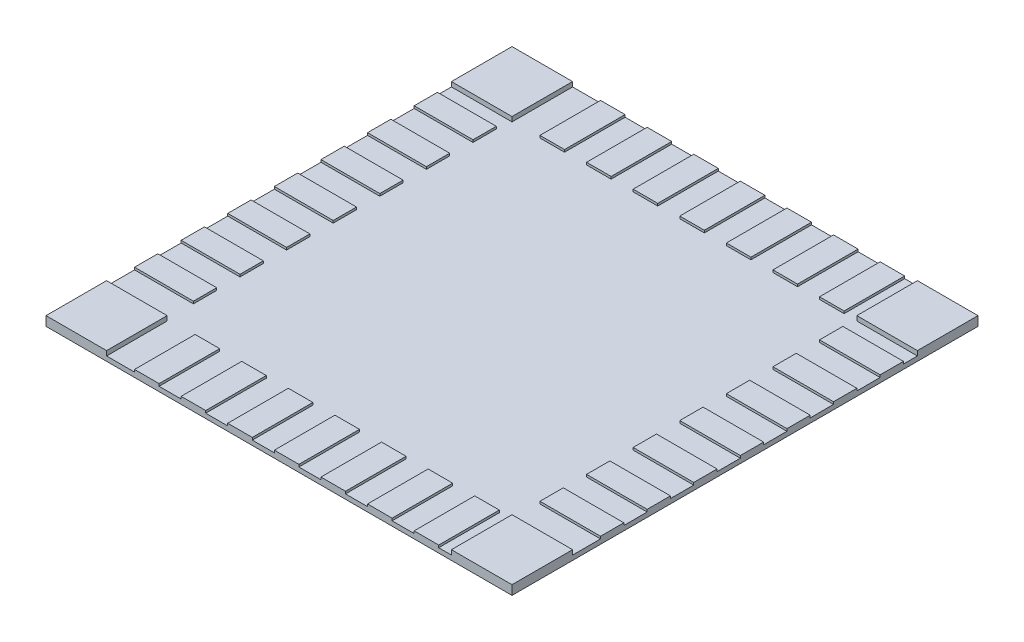
SolidWorks part; units mm, degrees
ref_plane "Plano frontal" through (0, 0, 0) normal (0, 0, 1) x (1, 0, 0)
ref_plane "Plano superior" through (0, 0, 0) normal (0, 1, 0) x (1, 0, 0)
ref_plane "Plano direito" through (0, 0, 0) normal (1, 0, 0) x (0, 0, -1)
sketch "Esboço1" plane through (0, 0, 0) normal (0, 1, 0) x (1, 0, 0)
  line L1 (-0.5, -0.5) -> (0.5, -0.5)
  line L2 (-0.5, -0.5) -> (-0.5, 0.5)
  line L3 (-0.5, 0.5) -> (0.5, 0.5)
  line L4 (0.5, -0.5) -> (0.5, 0.5)
  line L5 (-0.5, -0.5) -> (0.5, 0.5) construction
  line L6 (-0.5, 0.5) -> (0.5, -0.5) construction
  point P0 (0, 0)
  dimension "D1" = 1
  dimension "D2" = 1
sketch "Esboço2" plane through (0, 0, 0) normal (0, 1, 0) x (1, 0, 0)
  line L0 (-0.5, -0.5) -> (-0.5, -0.37)
  line L2 (0.5, 0.5) -> (0.5, 0.37)
  line L5 (-0.5, 0.5) -> (0.5, -0.5) construction
  line L6 (-0.5, -0.5) -> (-0.37, -0.5)
  line L10 (0.5, -0.5) -> (0.37, -0.5)
  line L11 (0.5, -0.5) -> (0.5, -0.37)
  line L12 (0.5, -0.37) -> (0.37, -0.37)
  line L13 (0.37, -0.5) -> (0.37, -0.37)
  line L14 (-0.5, -0.37) -> (-0.37, -0.37)
  line L15 (-0.37, -0.37) -> (-0.37, -0.5)
  line L16 (0.5, 0.37) -> (0.37, 0.37)
  line L17 (0.37, 0.37) -> (0.37, 0.5)
  line L18 (0.37, 0.5) -> (0.5, 0.5)
  line L19 (0.37, 0.37) -> (-0.37, 0.37) construction
  line L20 (-0.37, 0.37) -> (-0.5, 0.37)
  line L21 (-0.5, 0.37) -> (-0.5, 0.5)
  line L22 (-0.5, 0.5) -> (-0.37, 0.5)
  line L23 (-0.37, 0.37) -> (-0.37, 0.5)
  dimension "D1" = 0.13
  dimension "D2" = 0.13
  dimension "D3" = 0.13
  dimension "D4" = 0.13
  dimension "D5" = 0.13
extrude "Ressalto-extrusão1" add sketch "Esboço1" along normal blind 0.01
sketch "Esboço3" plane through (0, 0.01, 0) normal (0, 1, 0) x (1, 0, 0)
  line L0 (-0.31, -0.5) -> (-0.31, -0.37)
  line L1 (-0.5, -0.5) -> (0.5, -0.5) construction
  line L2 (0.5, -0.21) -> (0.5, -0.16)
  line L7 (-0.31, -0.37) -> (-0.2573, -0.37)
  line L8 (-0.2573, -0.37) -> (-0.2573, -0.5)
  line L10 (-0.2573, -0.5) -> (-0.31, -0.5)
  line L16 (-0.1573, -0.5) -> (-0.21, -0.5)
  line L17 (-0.21, -0.5) -> (-0.21, -0.37)
  line L41 (-0.21, -0.37) -> (-0.1573, -0.37)
  line L46 (-0.1573, -0.37) -> (-0.1573, -0.5)
  line L52 (-0.0573, -0.5) -> (-0.11, -0.5)
  line L53 (-0.11, -0.5) -> (-0.11, -0.37)
  line L54 (0.37, -0.16) -> (0.5, -0.16)
  line L62 (-0.11, -0.37) -> (-0.0573, -0.37)
  line L63 (-0.0573, -0.37) -> (-0.0573, -0.5)
  line L96 (0.0427, -0.5) -> (-0.01, -0.5)
  line L97 (-0.01, -0.5) -> (-0.01, -0.37)
  line L98 (-0.01, -0.37) -> (0.0427, -0.37)
  line L99 (0.0427, -0.37) -> (0.0427, -0.5)
  line L100 (0.1427, -0.5) -> (0.09, -0.5)
  line L101 (0.09, -0.5) -> (0.09, -0.37)
  line L102 (0.09, -0.37) -> (0.1427, -0.37)
  line L103 (0.1427, -0.37) -> (0.1427, -0.5)
  line L104 (0.2427, -0.5) -> (0.19, -0.5)
  line L105 (0.19, -0.5) -> (0.19, -0.37)
  line L106 (0.19, -0.37) -> (0.2427, -0.37)
  line L107 (0.2427, -0.37) -> (0.2427, -0.5)
  line L108 (0.3427, -0.5) -> (0.29, -0.5)
  line L109 (0.29, -0.5) -> (0.29, -0.37)
  line L110 (0.29, -0.37) -> (0.3427, -0.37)
  line L111 (0.3427, -0.37) -> (0.3427, -0.5)
  line L112 (-0.37, -0.37) -> (-0.37, -0.5) construction
  line L113 (0.5, -0.31) -> (0.37, -0.31)
  line L114 (0.5, -0.5) -> (0.5, 0.5) construction
  line L115 (0.5, -0.37) -> (0.37, -0.37) construction
  line L116 (0.37, -0.31) -> (0.37, -0.26)
  line L117 (0.37, -0.26) -> (0.5, -0.26)
  line L118 (0.5, -0.31) -> (0.5, -0.26)
  line L119 (0.37, -0.21) -> (0.37, -0.16)
  line L120 (0.5, -0.21) -> (0.37, -0.21)
  line L121 (0.5, -0.11) -> (0.5, -0.06)
  line L122 (0.37, -0.06) -> (0.5, -0.06)
  line L123 (0.37, -0.11) -> (0.37, -0.06)
  line L124 (0.5, -0.11) -> (0.37, -0.11)
  line L125 (0.5, -0.01) -> (0.5, 0.04)
  line L126 (0.37, 0.04) -> (0.5, 0.04)
  line L127 (0.37, -0.01) -> (0.37, 0.04)
  line L128 (0.5, -0.01) -> (0.37, -0.01)
  line L129 (0.5, 0.09) -> (0.5, 0.14)
  line L130 (0.37, 0.14) -> (0.5, 0.14)
  line L131 (0.37, 0.09) -> (0.37, 0.14)
  line L132 (0.5, 0.09) -> (0.37, 0.09)
  line L133 (0.5, 0.19) -> (0.5, 0.24)
  line L134 (0.37, 0.24) -> (0.5, 0.24)
  line L135 (0.37, 0.19) -> (0.37, 0.24)
  line L136 (0.5, 0.19) -> (0.37, 0.19)
  line L137 (0.5, 0.29) -> (0.5, 0.34)
  line L138 (0.37, 0.34) -> (0.5, 0.34)
  line L139 (0.37, 0.29) -> (0.37, 0.34)
  line L140 (0.5, 0.29) -> (0.37, 0.29)
  line L141 (0.3427, 0.5) -> (0.3427, 0.37)
  line L142 (0.5, 0.5) -> (-0.5, 0.5) construction
  line L143 (0.37, 0.37) -> (-0.37, 0.37) construction
  line L144 (0.3427, 0.37) -> (0.29, 0.37)
  line L145 (0.29, 0.37) -> (0.29, 0.5)
  line L146 (0.29, 0.5) -> (0.3427, 0.5)
  line L147 (0.19, 0.5) -> (0.2427, 0.5)
  line L148 (0.2427, 0.5) -> (0.2427, 0.37)
  line L149 (0.2427, 0.37) -> (0.19, 0.37)
  line L150 (0.19, 0.37) -> (0.19, 0.5)
  line L151 (0.09, 0.5) -> (0.1427, 0.5)
  line L152 (0.1427, 0.5) -> (0.1427, 0.37)
  line L153 (0.1427, 0.37) -> (0.09, 0.37)
  line L154 (0.09, 0.37) -> (0.09, 0.5)
  line L155 (-0.01, 0.5) -> (0.0427, 0.5)
  line L156 (0.0427, 0.5) -> (0.0427, 0.37)
  line L157 (0.0427, 0.37) -> (-0.01, 0.37)
  line L158 (-0.01, 0.37) -> (-0.01, 0.5)
  line L159 (-0.11, 0.5) -> (-0.0573, 0.5)
  line L160 (-0.0573, 0.5) -> (-0.0573, 0.37)
  line L161 (-0.0573, 0.37) -> (-0.11, 0.37)
  line L162 (-0.11, 0.37) -> (-0.11, 0.5)
  line L163 (-0.21, 0.5) -> (-0.1573, 0.5)
  line L164 (-0.1573, 0.5) -> (-0.1573, 0.37)
  line L165 (-0.1573, 0.37) -> (-0.21, 0.37)
  line L166 (-0.21, 0.37) -> (-0.21, 0.5)
  line L167 (-0.31, 0.5) -> (-0.2573, 0.5)
  line L168 (-0.2573, 0.5) -> (-0.2573, 0.37)
  line L169 (-0.2573, 0.37) -> (-0.31, 0.37)
  line L170 (-0.31, 0.37) -> (-0.31, 0.5)
  line L171 (-0.5, 0.34) -> (-0.3737, 0.34)
  line L172 (-0.5, 0.5) -> (-0.5, -0.5) construction
  line L173 (-0.3737, 0.34) -> (-0.3737, 0.29)
  line L174 (-0.3737, 0.29) -> (-0.5, 0.29)
  line L175 (-0.5, 0.29) -> (-0.5, 0.34)
  line L176 (-0.5, 0.19) -> (-0.5, 0.24)
  line L177 (-0.5, 0.24) -> (-0.3737, 0.24)
  line L178 (-0.3737, 0.24) -> (-0.3737, 0.19)
  line L179 (-0.3737, 0.19) -> (-0.5, 0.19)
  line L180 (-0.5, 0.09) -> (-0.5, 0.14)
  line L181 (-0.5, 0.14) -> (-0.3737, 0.14)
  line L182 (-0.3737, 0.14) -> (-0.3737, 0.09)
  line L183 (-0.3737, 0.09) -> (-0.5, 0.09)
  line L184 (-0.5, -0.01) -> (-0.5, 0.04)
  line L185 (-0.5, 0.04) -> (-0.3737, 0.04)
  line L186 (-0.3737, 0.04) -> (-0.3737, -0.01)
  line L187 (-0.3737, -0.01) -> (-0.5, -0.01)
  line L188 (-0.5, -0.11) -> (-0.5, -0.06)
  line L189 (-0.5, -0.06) -> (-0.3737, -0.06)
  line L190 (-0.3737, -0.06) -> (-0.3737, -0.11)
  line L191 (-0.3737, -0.11) -> (-0.5, -0.11)
  line L192 (-0.5, -0.21) -> (-0.5, -0.16)
  line L193 (-0.5, -0.16) -> (-0.3737, -0.16)
  line L194 (-0.3737, -0.16) -> (-0.3737, -0.21)
  line L195 (-0.3737, -0.21) -> (-0.5, -0.21)
  line L196 (-0.5, -0.31) -> (-0.5, -0.26)
  line L197 (-0.5, -0.26) -> (-0.3737, -0.26)
  line L198 (-0.3737, -0.26) -> (-0.3737, -0.31)
  line L199 (-0.3737, -0.31) -> (-0.5, -0.31)
  dimension "D1" = 0.13
  dimension "D2" = 7
  dimension "D3" = 0.06
  dimension "D5" = 0.05
  dimension "D6" = 0.13
  dimension "D4" = 0.06
extrude "Ressalto-extrusão2" add sketch "Esboço3" along normal blind 0.005
extrude "Ressalto-extrusão4" add sketch "Esboço2" along normal blind 0.02
